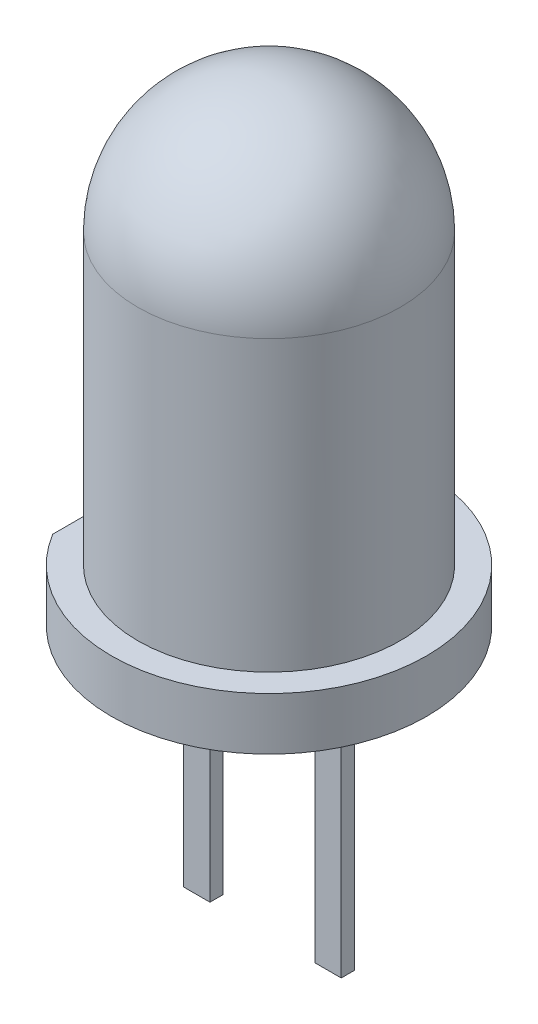
SolidWorks part; units mm, degrees
ref_plane "Front Plane" through (0, 0, 0) normal (0, 0, 1) x (1, 0, 0)
ref_plane "Top Plane" through (0, 0, 0) normal (0, 1, 0) x (1, 0, 0)
ref_plane "Right Plane" through (0, 0, 0) normal (1, 0, 0) x (0, 0, -1)
sketch "Sketch1" plane through (0, 0, 0) normal (0, 0, 1) x (1, 0, 0)
  line L0 (0, 40.4813) -> (0, -45.6712) construction
  line L3 (0, 2.5) -> (0, -5.5)
  line L5 (2.5, 0) -> (2.5, -5.5)
  line L6 (2.5, -5.5) -> (3, -5.5)
  line L7 (0, -5.5) -> (0, -6.5)
  line L8 (0, -6.5) -> (3, -6.5)
  line L9 (3, -5.5) -> (3, -6.5)
  arc A0 (2.5, 0) -> (0, 2.5) centre (0, 0) ccw
  dimension "D1" = 5
  dimension "D2" = 9
  dimension "D3" = 3
  dimension "D4" = 1
revolve "Revolve1" add sketch "Sketch1" angle 360 about L0
sketch "Sketch2" plane through (0, -6.5, 0) normal (0, -1, 0) x (1, 0, 0)
  line L0 (0, 0.7494) -> (0, -0.7682) construction
  line L1 (1, 0.125) -> (1.5, 0.125)
  line L2 (1, 0.125) -> (1, -0.125)
  line L3 (1, -0.125) -> (1.5, -0.125)
  line L4 (1.5, 0.125) -> (1.5, -0.125)
  line L5 (-1, 0.125) -> (-1, -0.125)
  line L6 (-1.5, 0.125) -> (-1.5, -0.125)
  line L7 (-1, -0.125) -> (-1.5, -0.125)
  line L8 (-1, 0.125) -> (-1.5, 0.125)
  point P5 (1, 0)
  dimension "D1" = 0.25
  dimension "D2" = 0.5
  dimension "D3" = 1
sketch "Sketch4" plane through (0, -6.5, 0) normal (0, -1, 0) x (1, 0, 0)
  line L1 (-2.5675, 1.75) -> (-3.0675, 1.75)
  line L2 (-2.5675, 1.75) -> (-2.5675, -1.75)
  line L3 (-2.5675, -1.75) -> (-3.0675, -1.75)
  line L4 (-3.0675, 1.75) -> (-3.0675, -1.75)
  point P4 (-2.5675, 0)
  dimension "D1" = 3.5
  dimension "D2" = 0.5
extrude "Extrude4" cut sketch "Sketch4" against normal blind 2
extrude "凸台-拉伸1" add sketch "Sketch2" along normal blind 5
